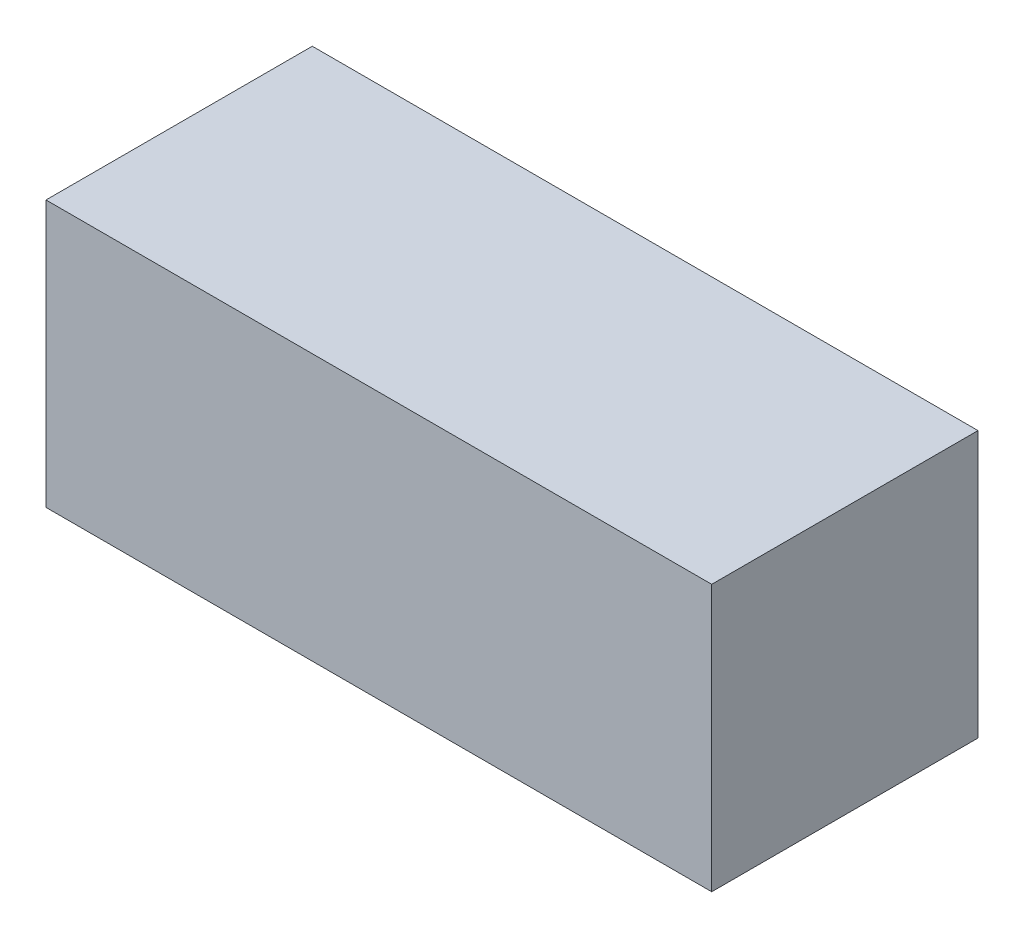
SolidWorks part; units mm, degrees
ref_plane "前视基准面" through (0, 0, 0) normal (0, 0, 1) x (1, 0, 0)
ref_plane "上视基准面" through (0, 0, 0) normal (0, 1, 0) x (1, 0, 0)
ref_plane "右视基准面" through (0, 0, 0) normal (1, 0, 0) x (0, 0, -1)
other "Configuration Table"
sketch "草图1" plane through (0, 0, 0) normal (0, 0, 1) x (1, 0, 0)
  line L1 (-11.3782, 8.763) -> (13.6218, 8.763)
  line L2 (-11.3782, 8.763) -> (-11.3782, -1.237)
  line L3 (-11.3782, -1.237) -> (13.6218, -1.237)
  line L4 (13.6218, 8.763) -> (13.6218, -1.237)
  dimension "D1" = 25
  dimension "D2" = 10
extrude "凸台-拉伸1" add sketch "草图1" along normal blind 10
